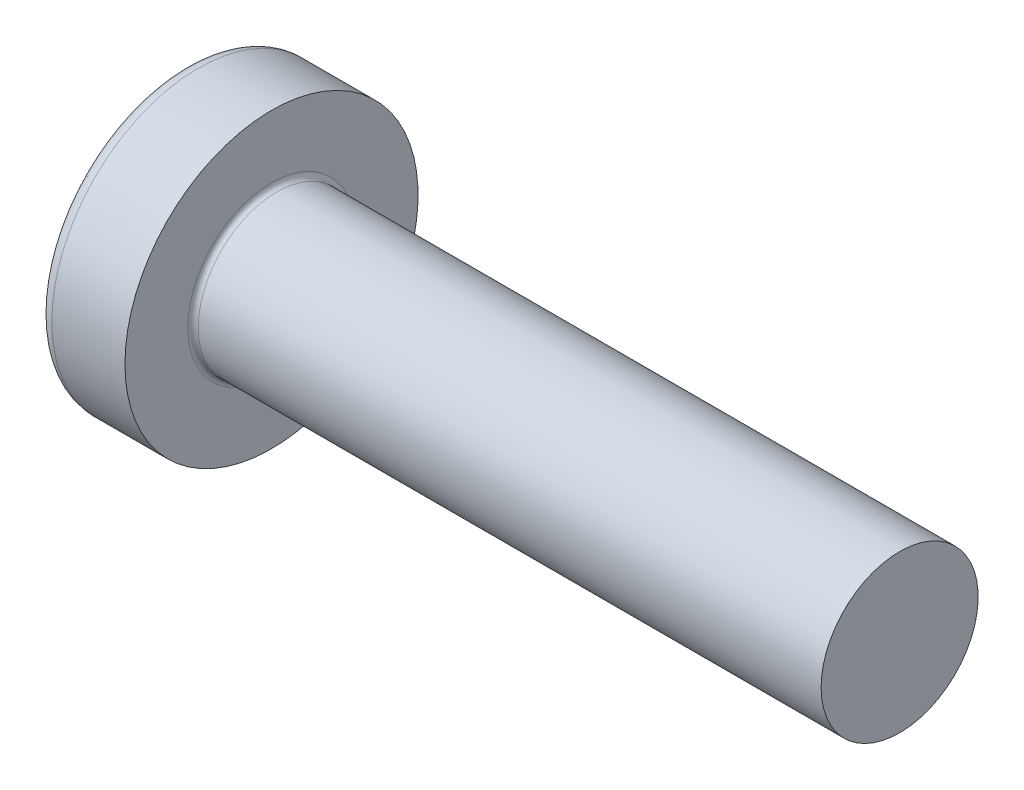
SolidWorks part; units mm, degrees
ref_plane "Plane1" through (0, 0, 0) normal (0, 0, 1) x (1, 0, 0)
ref_plane "Plane2" through (0, 0, 0) normal (0, 1, 0) x (1, 0, 0)
ref_plane "Plane3" through (0, 0, 0) normal (1, 0, 0) x (0, 0, -1)
sketch "BodySke" plane through (0, 0, 0) normal (0, 0, 1) x (1, 0, 0)
  line L0 (2.4, 1.5) -> (2.4, 2.8)
  line L1 (2.65, 6.35) -> (2.65, -3.175) construction
  line L2 (-25.4, 0) -> (127, 0) construction
  line L3 (14.4, 0) -> (0, 0)
  line L4 (2.4, 1.5) -> (14.4, 1.5)
  line L5 (14.4, 1.5) -> (14.4, 0)
  line L6 (1.0035, 2.8) -> (2.4, 2.8)
  line L8 (2.4, 6.35) -> (2.4, -3.175) construction
  arc A0 (0.7754, 2.6744) -> (0, 0) centre (5, 0) ccw
  arc A2 (0.7754, 2.6744) -> (1.0035, 2.8) centre (1.0035, 2.53) cw
  dimension "Head_crown_rad" = 5
  dimension "Head_fillet_rad" = 0.27
  dimension "Head_ht" = 2.4
  dimension "Head_dia" = 5.6
  dimension "Advance" = 0.5
  dimension "Diameter" = 3
revolve "Base-Revolve" add sketch "BodySke"
cosmetic thread "ThreadCosmetic" [suppressed]
fillet "Fillet1" radius 0.1 1 edges at (2.4, 0, 1.5)
sketch "Sketch3" plane through (0, 0, 0) normal (1, 0, 0) x (0, 0, -1)
  line L0 (0.37, -1.4) -> (-0.37, -1.4)
  line L1 (0.37, -1.4) -> (0.37, 1.4)
  line L2 (-0.37, 1.4) -> (0.37, 1.4)
  line L3 (-0.37, 1.4) -> (-0.37, -1.4)
  dimension "Cross_dia" = 2.8
  dimension "D1" = 1.4
  dimension "Cross_width" = 0.74
  dimension "D2" = 0.37
ref_plane "Plane4" through (1.75, 0, 0) normal (1, 0, 0) x (0, 0, -1)
sketch "Sketch4" plane through (1.75, 0, 0) normal (1, 0, 0) x (0, 0, -1)
  line L0 (0.37, -0.5275) -> (-0.37, -0.5275)
  line L1 (0.37, -0.5275) -> (0.37, 0.5275)
  line L2 (-0.37, 0.5275) -> (0.37, 0.5275)
  line L3 (-0.37, 0.5275) -> (-0.37, -0.5275)
  dimension "D1" = 0.74
  dimension "D2" = 1.055
  dimension "D3" = 0.37
  dimension "D4" = 0.5275
loft "Recess" cut profiles "Sketch3", "Sketch4"
pattern_circular "RecPat" count 2 every 90 about axis through (0, 0, 0) along (1, 0, 0) of "Recess"
sketch "RecCorSke" plane through (0, 0, 0) normal (0, 0, 1) x (1, 0, 0)
  line L0 (-3.175, 0) -> (15.875, 0) construction
  line L1 (-25.4, 0) -> (127, 0) construction
  line L2 (0, 0) -> (0, 0.6784)
  line L3 (0, 0.6784) -> (1.75, 0.556)
  line L4 (1.75, 0.556) -> (1.9307, 0)
  line L5 (1.9307, 0) -> (0, 0)
  dimension "Diameter" = 1.112
  dimension "Depth" = 1.75
  dimension "Draft_angle" = 4
  dimension "Bottom_angle" = 18
revolve "RecessCore" cut sketch "RecCorSke" angle 360 about L0
sketch "ThdSchSke" plane through (0, 0, 0) normal (0, 0, 1) x (1, 0, 0)
  line L0 (3.4, -1.2195) -> (3.2036, -1.5)
  line L1 (3.4, -1.2195) -> (3.5964, -1.5)
  line L2 (3.5964, -1.5) -> (3.5964, -1.875)
  line L3 (-3.175, 0) -> (5.1513, 0) construction
  line L5 (3.5964, -1.875) -> (3.2036, -1.875)
  line L6 (3.2036, -1.875) -> (3.2036, -1.5)
  dimension "Diameter" = 3
  dimension "SideAngle" = 55
  dimension "VeeAngle" = 70
  dimension "Thread_minor" = 2.439
  dimension "Overcut" = 3.75
  dimension "Start" = 3.4
revolve "ThreadSchematic" [suppressed] cut sketch "ThdSchSke" angle 360 about L3
pattern_linear "ThdSchPat" [suppressed]
equation "\"D1@Sketch3\" = \"Cross_dia@Sketch3\" / 2"
equation "\"D2@Sketch3\" = \"Cross_width@Sketch3\" / 2"
equation "\"Depth@RecCorSke\" = \"Cross_depth@Plane4\""
equation "\"D1@Sketch4\" = \"Cross_width@Sketch3\""
equation "\"D2@Sketch4\" = \"Cross_dia@Sketch3\" - 2.0 * \"Cross_depth@Plane4\" * tan(26.5  * 0.017453292)"
equation "\"D3@Sketch4\" = \"D1@Sketch4\" / 2"
equation "\"D4@Sketch4\" = \"D2@Sketch4\" / 2"
equation "\"Thread_length@ThreadCosmetic\" = ((sgn( (\"Length@BodySke\" - \"Advance@BodySke\" * 2.0 ) - \"Thread_nom@BodySke\" )-1)*( (\"Length@BodySke\" - \"Advance@BodySke\" * 2.0 ) - \"Thread_nom@BodySke\" ))/-2+ \"Thread_nom@BodySke\""
equation "\"Thread_minor@ThdSchSke\" = \"Thread_minor@ThreadCosmetic\""
equation "\"Diameter@ThdSchSke\" = \"Diameter@BodySke\""
equation "\"Overcut@ThdSchSke\" = \"Diameter@BodySke\" * 1.25"
equation "\"Start@ThdSchSke\" = \"Head_ht@BodySke\" + \"Length@BodySke\" - \"Thread_length@ThreadCosmetic\"  '---Non-countersunk---"
equation "\"Num_threads@ThdSchPat\" = int( \"Thread_length@ThreadCosmetic\" / \"Advance@BodySke\" + 0.999 )  + 1"
equation "\"Advance@ThdSchPat\" = \"Thread_length@ThreadCosmetic\" /  (\"Num_threads@ThdSchPat\" - 1) 'relax it"
